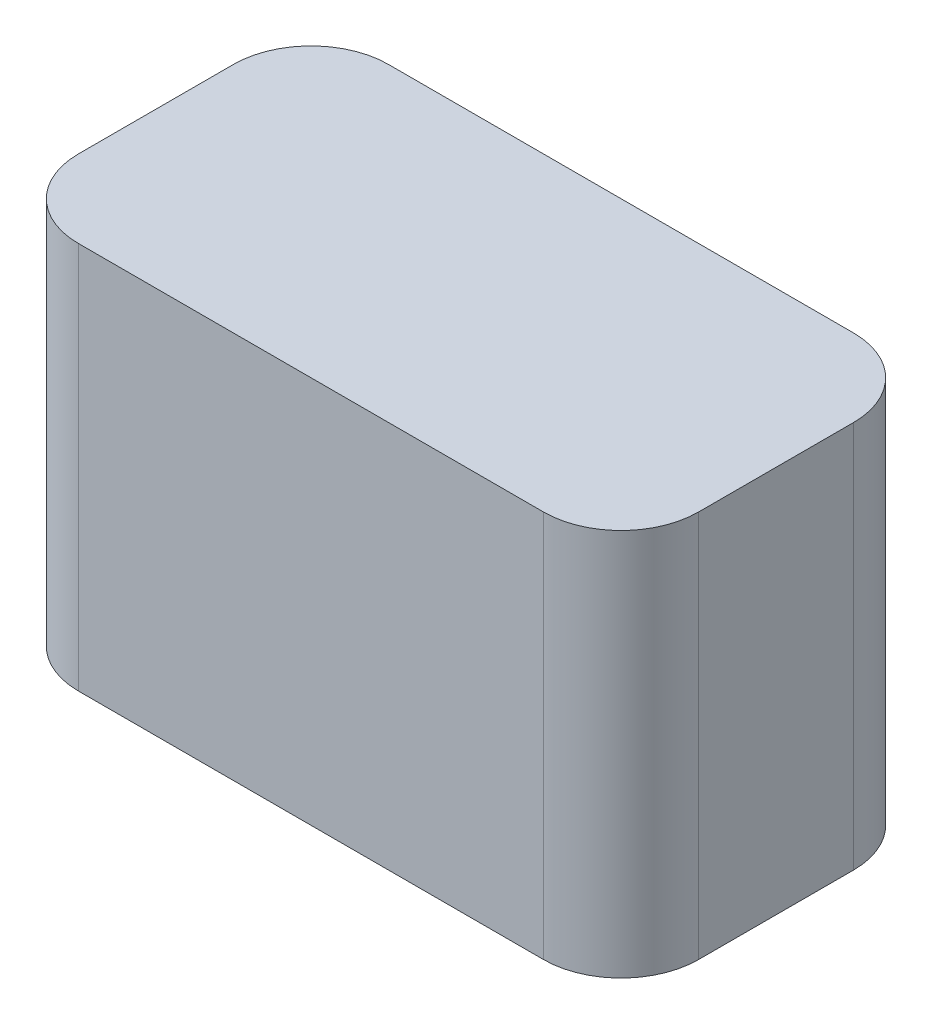
SolidWorks part; units mm, degrees
ref_plane "Front Plane" through (0, 0, 0) normal (0, 0, 1) x (1, 0, 0)
ref_plane "Top Plane" through (0, 0, 0) normal (0, 1, 0) x (1, 0, 0)
ref_plane "Right Plane" through (0, 0, 0) normal (1, 0, 0) x (0, 0, -1)
sketch "Sketch1" plane through (0, 0, 0) normal (0, 1, 0) x (1, 0, 0)
  line L1 (-3, 2) -> (3, 2)
  line L2 (-4, 1) -> (-4, -1)
  line L3 (-3, -2) -> (3, -2)
  line L4 (4, 1) -> (4, -1)
  line L5 (-4, 2) -> (4, -2) construction
  line L6 (-4, -2) -> (4, 2) construction
  arc A0 (-3, 2) -> (-4, 1) centre (-3, 1) ccw
  arc A1 (-4, -1) -> (-3, -2) centre (-3, -1) ccw
  arc A2 (3, 2) -> (4, 1) centre (3, 1) cw
  arc A3 (4, -1) -> (3, -2) centre (3, -1) cw
  point P0 (0, 0)
  dimension "D3" = 1
  dimension "D4" = 1
  dimension "D5" = 1
  dimension "D6" = 1
  dimension "D1" = 8
  dimension "D2" = 4
extrude "Boss-Extrude1" add sketch "Sketch1" along normal blind 5
